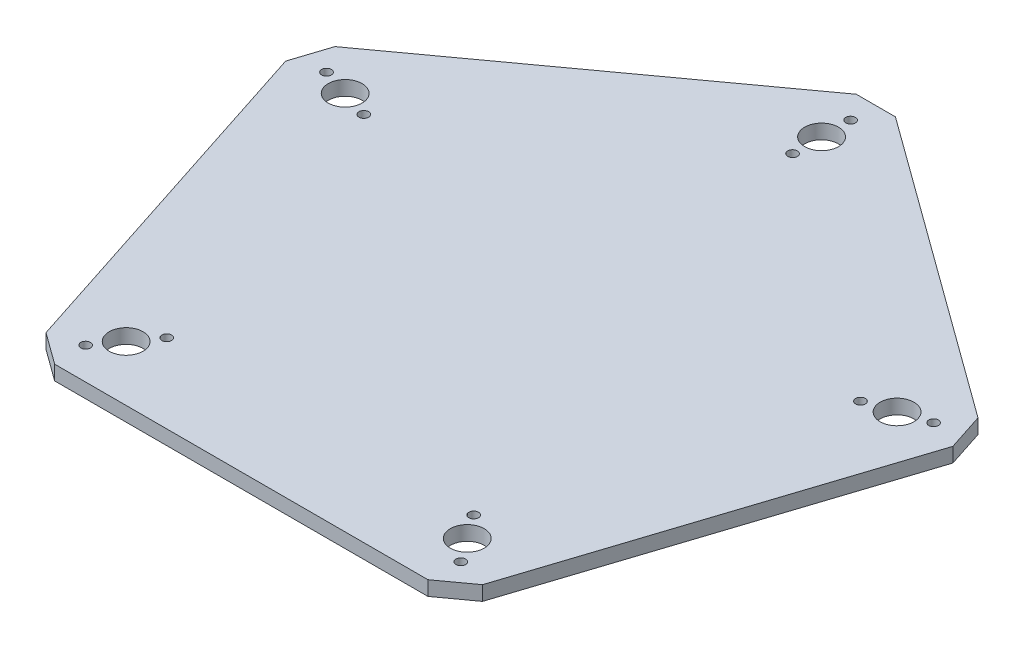
SolidWorks part; units mm, degrees
ref_plane "Plan de face" through (0, 0, 0) normal (0, 0, 1) x (1, 0, 0)
ref_plane "Plan de dessus" through (0, 0, 0) normal (0, 1, 0) x (1, 0, 0)
ref_plane "Plan de droite" through (0, 0, 0) normal (1, 0, 0) x (0, 0, -1)
sketch "Esquisse2" plane through (0, 0, 0) normal (0, 1, 0) x (1, 0, 0)
  line L1 (70.5342, 22.918) -> (0, 74.1641)
  line L2 (0, 74.1641) -> (-70.5342, 22.918)
  line L3 (-70.5342, 22.918) -> (-43.5926, -60)
  line L4 (-43.5926, -60) -> (43.5926, -60)
  line L5 (43.5926, -60) -> (70.5342, 22.918)
  line L26 (-70.5342, 22.918) -> (0, 0) construction
  line L27 (-57.0634, 18.541) -> (-59.0076, 12.5574) construction
  circle A0 centre (-57.0634, 18.541) radius 3.5
  circle A1 centre (0, 0) radius 60 construction
  circle A2 centre (0, 60) radius 3.5
  circle A3 centre (57.0634, 18.541) radius 3.5
  circle A4 centre (35.2671, -48.541) radius 3.5
  circle A5 centre (-35.2671, -48.541) radius 3.5
  circle A6 centre (-62.7697, 20.3951) radius 1
  circle A7 centre (-51.3571, 16.6869) radius 1
  circle A8 centre (0, 66) radius 1
  circle A9 centre (0, 54) radius 1
  circle A10 centre (62.7697, 20.3951) radius 1
  circle A11 centre (51.3571, 16.6869) radius 1
  circle A12 centre (38.7938, -53.3951) radius 1
  circle A13 centre (31.7404, -43.6869) radius 1
  circle A14 centre (-38.7938, -53.3951) radius 1
  circle A15 centre (-31.7404, -43.6869) radius 1
  point P32 (0, 0)
  point P43 (0, 0)
  point P65 (0, 0)
  point P109 (0, 0)
  dimension "D1" = 120
  dimension "D7" = 7
  dimension "D8" = 5
  dimension "D9" = 2
  dimension "D11" = 5
  dimension "D2" = 6
extrude "Boss.-Extru.1" add sketch "Esquisse2" along normal blind 3
sketch "Esquisse4" plane through (0, 0, 0) normal (0, -1, 0) x (1, 0, 0)
chamfer "Chanfrein1" distance 5 5 edges at (-43.5926, 1.5, 60) (43.5926, 1.5, 60) (70.5342, 1.5, -22.918) (0, 1.5, -74.1641) (-70.5342, 1.5, -22.918)
